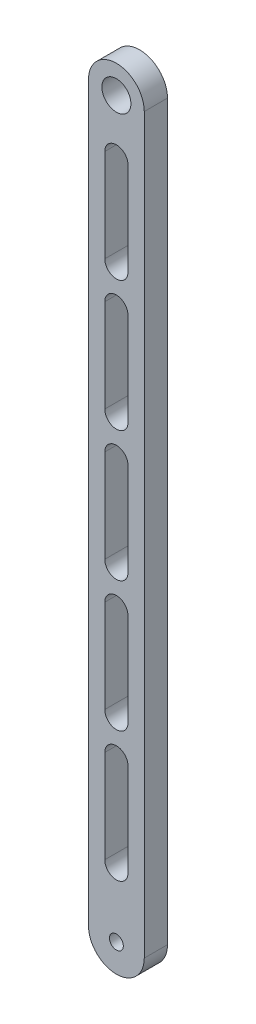
SolidWorks part; units mm, degrees
ref_plane "前视基准面" through (0, 0, 0) normal (0, 0, 1) x (1, 0, 0)
ref_plane "上视基准面" through (0, 0, 0) normal (0, 1, 0) x (1, 0, 0)
ref_plane "右视基准面" through (0, 0, 0) normal (1, 0, 0) x (0, 0, -1)
other "Configuration Table"
sketch "草图2" plane through (0, 0, 0) normal (0, 0, 1) x (1, 0, 0)
  line L0 (0, 0) -> (0, 200.3806) construction
  line L1 (-7.62, 0) -> (-7.62, 200.3806)
  line L2 (7.62, 0) -> (7.62, 200.3806)
  line L3 (0, 185.5216) -> (0, 160.1216) construction
  line L4 (3.175, 185.5216) -> (3.175, 160.1216)
  line L5 (-3.175, 185.5216) -> (-3.175, 160.1216)
  line L8 (0, 149.9616) -> (0, 124.5616) construction
  line L11 (3.175, 149.9616) -> (3.175, 124.5616)
  line L14 (-3.175, 149.9616) -> (-3.175, 124.5616)
  line L15 (-3.175, 185.5216) -> (-3.175, 134.7216) construction
  line L16 (0, 114.4016) -> (0, 89.0016) construction
  line L17 (3.175, 114.4016) -> (3.175, 89.0016)
  line L18 (-3.175, 114.4016) -> (-3.175, 89.0016)
  line L19 (0, 78.8416) -> (0, 53.4416) construction
  line L20 (3.175, 78.8416) -> (3.175, 53.4416)
  line L21 (-3.175, 78.8416) -> (-3.175, 53.4416)
  line L22 (0, 43.2816) -> (0, 17.8816) construction
  line L23 (3.175, 43.2816) -> (3.175, 17.8816)
  line L24 (-3.175, 43.2816) -> (-3.175, 17.8816)
  line L25 (0, 185.5216) -> (0, 149.9616) construction
  arc A0 (-7.62, 0) -> (7.62, 0) centre (0, 0) ccw
  arc A1 (7.62, 200.3806) -> (-7.62, 200.3806) centre (0, 200.3806) ccw
  arc A4 (3.175, 185.5216) -> (-3.175, 185.5216) centre (0, 185.5216) ccw
  arc A5 (-3.175, 160.1216) -> (3.175, 160.1216) centre (0, 160.1216) ccw
  arc A6 (3.175, 149.9616) -> (-3.175, 149.9616) centre (0, 149.9616) ccw
  arc A7 (-3.175, 124.5616) -> (3.175, 124.5616) centre (0, 124.5616) ccw
  arc A8 (3.175, 114.4016) -> (-3.175, 114.4016) centre (0, 114.4016) ccw
  arc A9 (-3.175, 89.0016) -> (3.175, 89.0016) centre (0, 89.0016) ccw
  arc A10 (3.175, 78.8416) -> (-3.175, 78.8416) centre (0, 78.8416) ccw
  arc A11 (-3.175, 53.4416) -> (3.175, 53.4416) centre (0, 53.4416) ccw
  arc A12 (3.175, 43.2816) -> (-3.175, 43.2816) centre (0, 43.2816) ccw
  arc A13 (-3.175, 17.8816) -> (3.175, 17.8816) centre (0, 17.8816) ccw
  circle A15 centre (0, 200.3806) radius 3.9675
  point P2 (0, 100.1903)
  point P13 (0, 172.8216)
  point P21 (0, 137.2616)
  point P28 (0, 101.7016)
  point P35 (0, 66.1416)
  point P44 (0, 30.5816)
  dimension "D4" = 7.935
  dimension "D1" = 200.3806
  dimension "D2" = 15.24
  dimension "D5" = 25.4
  dimension "D6" = 6.35
  dimension "D8" = 35.56
  dimension "D9" = 14.859
  dimension "D10" = 17.8816
  dimension "D7" = 5
extrude "凸台-拉伸1" add sketch "草图2" along normal blind 6.35
sketch "Sketch1" plane through (0, 0, 6.35) normal (0, 0, 1) x (1, 0, 0)
  point P0 (0, 0)
hole_wizard "#10-24 Tapped Hole1" positions "Sketch1" profile "Sketch2" tap size "#10-24" standard "ANSI Inch" end condition through all
sketch "Sketch2" plane through (0, 0, 6.35) normal (1, 0, 0) x (0, -1, 0)
  line L0 (0, 0) -> (0, 6.35)
  line L1 (0, 6.35) -> (1.8986, 6.35)
  line L2 (1.8986, 6.35) -> (1.8986, 0)
  line L5 (1.8986, 0) -> (0, 0)
  line L11 (0, -6.35) -> (0, 107.95) construction
  dimension "Thru Tap Drill Dia." = 3.7973
  dimension "Thru Tap Drill Depth" = 6.35
cosmetic thread "Hole Thread1" parameters "D2"=4.826
